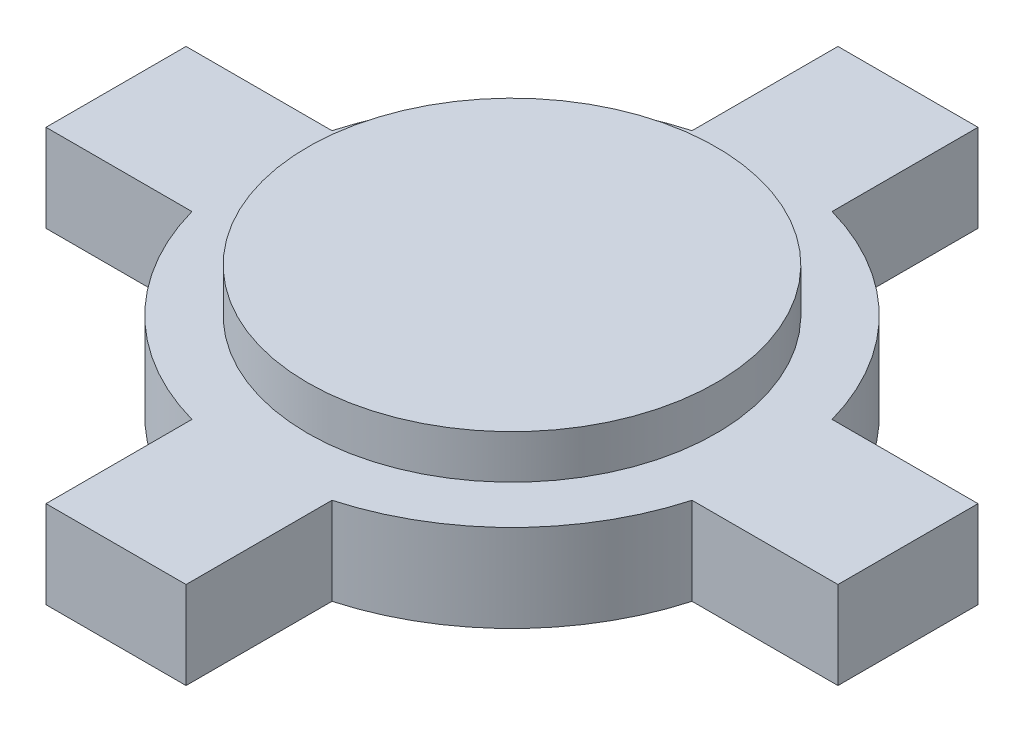
SolidWorks part; units mm, degrees
ref_plane "前视基准面" through (0, 0, 0) normal (0, 0, 1) x (1, 0, 0)
ref_plane "上视基准面" through (0, 0, 0) normal (0, 1, 0) x (1, 0, 0)
ref_plane "右视基准面" through (0, 0, 0) normal (1, 0, 0) x (0, 0, -1)
other "Configuration Table"
sketch "草图1" plane through (0, 0, 0) normal (0, 1, 0) x (1, 0, 0)
  line L0 (0, 7.9747) -> (0, -8.6444) construction
  line L1 (-13.5703, 2.4) -> (-8.5703, 2.4)
  line L2 (-13.5703, 2.4) -> (-13.5703, -2.4)
  line L3 (-13.5703, -2.4) -> (-8.5703, -2.4)
  line L4 (13.5703, 2.4) -> (13.5703, -2.4)
  line L5 (-2.4, 13.5703) -> (2.4, 13.5703)
  line L6 (-2.4, 13.5703) -> (-2.4, 8.5703)
  line L7 (-2.4, -13.5703) -> (2.4, -13.5703)
  line L8 (2.4, 13.5703) -> (2.4, 8.5703)
  line L13 (-10.8789, 0) -> (11.1113, 0) construction
  line L15 (-2.4, -8.5703) -> (-2.4, -13.5703)
  line L16 (8.5703, 2.4) -> (13.5703, 2.4)
  line L17 (8.5703, -2.4) -> (13.5703, -2.4)
  line L18 (2.4, -8.5703) -> (2.4, -13.5703)
  arc A0 (-2.4, 8.5703) -> (-8.5703, 2.4) centre (0, 0) ccw
  arc A1 (8.5703, 2.4) -> (2.4, 8.5703) centre (0, 0) ccw
  arc A2 (2.4, -8.5703) -> (8.5703, -2.4) centre (0, 0) ccw
  arc A3 (-8.5703, -2.4) -> (-2.4, -8.5703) centre (0, 0) ccw
  dimension "D1" = 17.8
  dimension "D2" = 4.8
  dimension "D3" = 5
extrude "凸台-拉伸1" add sketch "草图1" along normal blind 3
sketch "草图2" plane through (0, 3, 0) normal (0, 1, 0) x (1, 0, 0)
  circle A0 centre (0, 0) radius 7
  dimension "D1" = 14
extrude "凸台-拉伸2" add sketch "草图2" along normal blind 1.5
